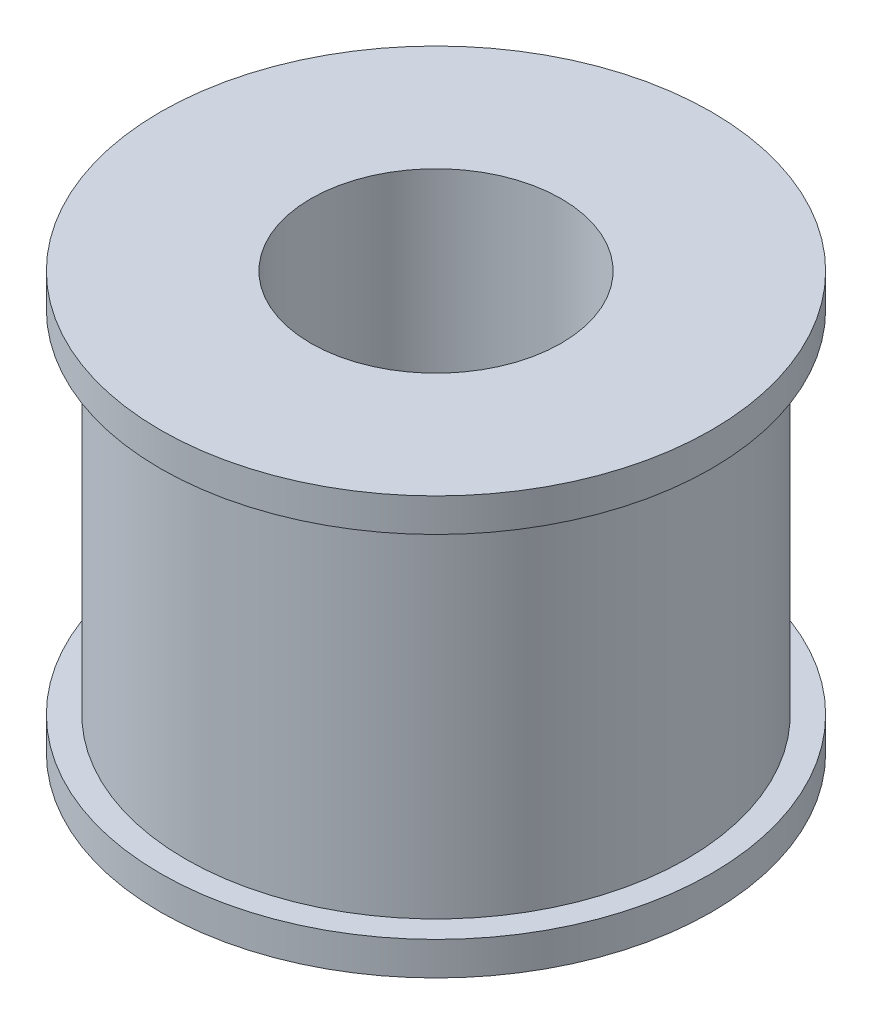
SolidWorks part; units mm, degrees
ref_plane "Alzado" through (0, 0, 0) normal (0, 0, 1) x (1, 0, 0)
ref_plane "Planta" through (0, 0, 0) normal (0, 1, 0) x (1, 0, 0)
ref_plane "Vista lateral" through (0, 0, 0) normal (1, 0, 0) x (0, 0, -1)
sketch "Croquis1" plane through (0, 0, 0) normal (0, 1, 0) x (1, 0, 0)
  circle A0 centre (0, 0) radius 3
  circle A1 centre (0, 0) radius 15
  dimension "D1" = 6
  dimension "D2" = 30
extrude "Saliente-Extruir1" add sketch "Croquis1" along normal blind 25
sketch "Croquis2" plane through (0, 0, 0) normal (0, -1, 0) x (1, 0, 0)
  circle A0 centre (0, 0) radius 3
  circle A1 centre (0, 0) radius 16.5
  dimension "D1" = 33
extrude "Saliente-Extruir2" add sketch "Croquis2" against normal blind 2
sketch "Croquis3" plane through (0, 25, 0) normal (0, 1, 0) x (1, 0, 0)
  circle A0 centre (0, 0) radius 3
  circle A1 centre (0, 0) radius 16.5
  dimension "D1" = 33
extrude "Saliente-Extruir3" add sketch "Croquis3" against normal blind 2
sketch "Croquis4" plane through (0, 0, 0) normal (0, 0, 1) x (1, 0, 0)
  line L2 (-16.5, 0) -> (16.5, 0) construction
  circle A0 centre (0, 5) radius 1.625
  dimension "D1" = 3.25
  dimension "D2" = 5
extrude "Cortar-Extruir1" cut sketch "Croquis4" against normal up to next
sketch "Croquis5" plane through (0, 25, 0) normal (0, 1, 0) x (1, 0, 0)
  circle A0 centre (0, 0) radius 7.5
  dimension "D1" = 15
extrude "Cortar-Extruir2" cut sketch "Croquis5" against normal blind 16
